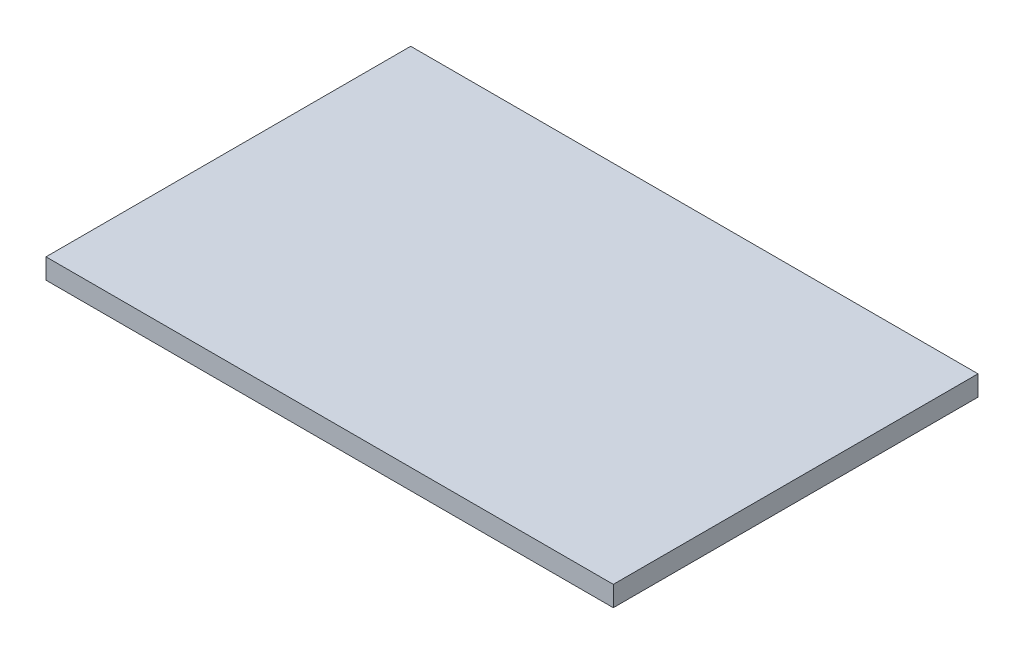
SolidWorks part; units mm, degrees
ref_plane "Front Plane" through (0, 0, 0) normal (0, 0, 1) x (1, 0, 0)
ref_plane "Top Plane" through (0, 0, 0) normal (0, 1, 0) x (1, 0, 0)
ref_plane "Right Plane" through (0, 0, 0) normal (1, 0, 0) x (0, 0, -1)
sketch "Sketch1" plane through (0, 0, 0) normal (0, 1, 0) x (1, 0, 0)
  line L1 (0, 0) -> (7, 0)
  line L2 (0, 0) -> (0, 4.5)
  line L3 (0, 4.5) -> (7, 4.5)
  line L4 (7, 0) -> (7, 4.5)
extrude "Boss-Extrude1" add sketch "Sketch1" along normal blind 0.25
sketch "Sketch2" plane through (0, 0.25, 0) normal (0, 1, 0) x (1, 0, 0)
  line L0 (0, 0) -> (7, 0) construction
  line L1 (1.143, 0) -> (2.0928, 0)
  line L2 (1.143, 0) -> (1.143, 0.6316)
  line L3 (1.143, 0.6316) -> (2.0928, 0.6316)
  line L4 (2.0928, 0) -> (2.0928, 0.6316)
